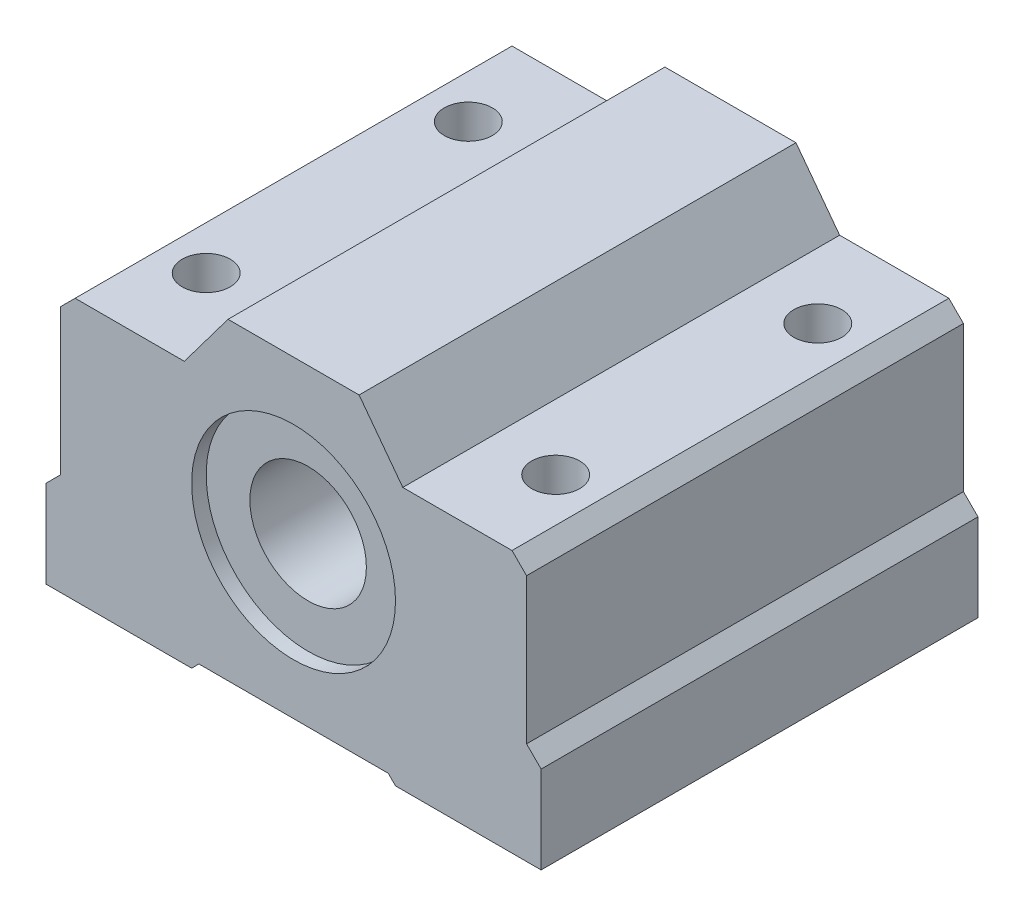
SolidWorks part; units mm, degrees
ref_plane "Front" through (0, 0, 0) normal (0, 0, 1) x (1, 0, 0)
ref_plane "Top" through (0, 0, 0) normal (0, 1, 0) x (1, 0, 0)
ref_plane "Right" through (0, 0, 0) normal (1, 0, 0) x (0, 0, -1)
sketch "Sketch1" plane through (0, 0, 0) normal (0, 0, 1) x (1, 0, 0)
  line L2 (-17, -2.4052) -> (-17, -8.4052)
  line L3 (-17, -8.4052) -> (-7, -8.4052)
  line L4 (-7, -8.4052) -> (-6.5, -7.9052)
  line L5 (-6.5, -7.9052) -> (6.5, -7.9052)
  line L6 (6.5, -7.9052) -> (7, -8.4052)
  line L7 (-17, -2.4052) -> (-16, -1.4052)
  line L8 (7, -8.4052) -> (17, -8.4052)
  line L9 (17, -8.4052) -> (17, -2.4052)
  line L15 (-16, -1.4052) -> (-16, 8.5948)
  line L16 (-16, 8.5948) -> (-15, 9.5948)
  line L17 (-15, 9.5948) -> (-7.5, 9.5948)
  line L21 (7.5, 9.5948) -> (15, 9.5948)
  line L22 (15, 9.5948) -> (16, 8.5948)
  line L23 (16, 8.5948) -> (16, -1.4052)
  line L24 (16, -1.4052) -> (17, -2.4052)
  line L25 (-7.5, 9.5948) -> (-4.5, 13.5948)
  line L26 (-4.5, 13.5948) -> (4.5, 13.5948)
  line L27 (4.5, 13.5948) -> (7.5, 9.5948)
  point P0 (0, -7.9052)
  point P19 (0, 3.0948)
  dimension "D1" = 34
  dimension "D2" = 32
  dimension "D3" = 0.5
  dimension "D4" = 10
  dimension "D5" = 0.5
  dimension "D6" = 6
  dimension "D7" = 15
  dimension "D8" = 30
  dimension "D9" = 9
  dimension "D10" = 22
  dimension "D11" = 18
  dimension "D12" = 11
extrude "Boss-Extrude1" add sketch "Sketch1" along normal blind 30
sketch "Sketch2" plane through (0, 0, 0) normal (0, 0, -1) x (-1, 0, 0)
  line L0 (17, -8.4052) -> (7, -8.4052) construction
  line L1 (6.5, -7.9052) -> (-6.5, -7.9052) construction
  circle A0 centre (0, 2.5948) radius 4
  point P7 (0, -7.9052)
  dimension "D1" = 8
  dimension "D2" = 11
extrude "Cut-Extrude1" cut sketch "Sketch2" against normal through all
sketch "Sketch3" plane through (0, 0, 0) normal (0, 0, -1) x (-1, 0, 0)
  circle A0 centre (0, 2.5948) radius 7
  dimension "D1" = 14
extrude "Cut-Extrude2" cut sketch "Sketch3" against normal blind 1
sketch "Sketch4" plane through (0, 0, 30) normal (0, 0, 1) x (1, 0, 0)
  circle A1 centre (0, 2.5948) radius 7
  circle A2 centre (0, 2.5948) radius 7
  dimension "D1" = 0
extrude "Cut-Extrude3" cut sketch "Sketch4" against normal blind 1
sketch "Sketch5" plane through (0, -8.4052, 0) normal (0, -1, 0) x (1, 0, 0)
  line L1 (-12, 24) -> (12, 24) construction
  line L2 (-12, 24) -> (-12, 6) construction
  line L3 (-12, 6) -> (12, 6) construction
  line L4 (12, 24) -> (12, 6) construction
  line L5 (-12, 24) -> (12, 6) construction
  line L6 (-12, 6) -> (12, 24) construction
  line L10 (-6.5, 0) -> (6.5, 0)
  line L11 (6.5, 0) -> (6.5, 30)
  line L12 (6.5, 30) -> (-6.5, 30)
  line L13 (-6.5, 30) -> (-6.5, 0)
  line L14 (-6.5, 0) -> (6.5, 0)
  line L15 (6.5, 0) -> (6.5, 30)
  line L16 (6.5, 30) -> (-6.5, 30)
  line L17 (-6.5, 30) -> (-6.5, 0)
  point P0 (0, 15)
  point P10 (-6.5, 15)
  point P13 (0, 0)
  dimension "D1" = 24
  dimension "D2" = 18
  dimension "D3" = 0
hole_wizard "Tap Drill for M4x0.7 Tap1" positions "Sketch6" profile "Sketch7" hole size "M4x0.7" standard "ANSI Metric" end condition through all
sketch "Sketch6" plane through (0, -8.4052, 0) normal (0, -1, 0) x (-1, 0, 0)
  point P0 (-12, -6)
  point P3 (12, -6)
  point P6 (12, -24)
  point P9 (-12, -24)
sketch "Sketch7" plane through (12, -8.4052, 6) normal (1, 0, 0) x (0, 0, -1)
  line L0 (0, 0) -> (0, 22)
  line L1 (0, 22) -> (1.65, 22)
  line L2 (1.65, 22) -> (1.65, 0)
  line L5 (1.65, 0) -> (0, 0)
  line L11 (0, -6.35) -> (0, 107.95) construction
  dimension "Thru Hole Dia." = 3.3
  dimension "Thru Hole Depth" = 22
